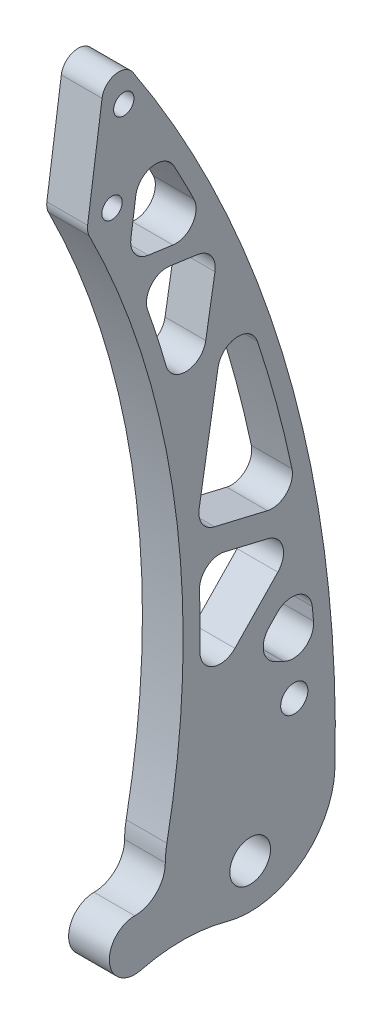
SolidWorks part; units mm, degrees
material "6061-T6 (SS)"
ref_plane "Front Plane" through (0, 0, 0) normal (0, 0, 1) x (1, 0, 0)
ref_plane "Top Plane" through (0, 0, 0) normal (0, 1, 0) x (1, 0, 0)
ref_plane "Right Plane" through (0, 0, 0) normal (1, 0, 0) x (0, 0, -1)
sketch "Sketch1" plane through (0, 0, 0) normal (1, 0, 0) x (0, 0, -1)
  line L0 (0, 0) -> (0, 200) construction
  line L1 (0, 0) -> (-44.9902, 194.874) construction
  line L2 (-41.8588, 217.155) -> (-48.1216, 172.593)
  circle A0 centre (0, -12) radius 6
  circle A1 centre (0, 0) radius 25
  arc A2 (24.9928, -0.6007) -> (-41.8588, 217.155) centre (-334.9033, 8.0499) ccw
  arc A3 (-24.539, 4.7789) -> (-48.1216, 172.593) centre (-279.7445, 54.4794) ccw
  dimension "D2" = 12
  dimension "D3" = 50
  dimension "D5" = 360
  dimension "D6" = 260
  dimension "D1" = 200
  dimension "D4" = 13
  dimension "D7" = 45
  dimension "D8" = 8
  dimension "D9" = 12
extrude "Boss-Extrude1" add sketch "Sketch1" along normal blind 12
sketch "Sketch3" plane through (12, 0, 0) normal (1, 0, 0) x (0, 0, -1)
  line L0 (-30.6472, 246.6326) -> (-44.1841, 150.313) construction
  line L1 (-41.8588, 217.155) -> (-48.1216, 172.593) construction
  circle A0 centre (-40.7145, 175) radius 3
  circle A1 centre (-37.2352, 199.7567) radius 3
  dimension "D2" = 6
  dimension "D1" = 25
  dimension "D3" = 7
  dimension "D4" = 175
extrude "Cut-Extrude2" cut sketch "Sketch3" against normal through all
sketch "Sketch4" plane through (12, 0, 0) normal (1, 0, 0) x (0, 0, -1)
  line L0 (-31.2609, 191.9692) -> (-35.9768, 158.4135)
  line L1 (-41.8588, 217.155) -> (-48.1216, 172.593) construction
  line L2 (-35.9768, 158.4135) -> (-11.7498, 155.0086)
  line L3 (-33.7602, 153.0529) -> (-9.3543, 149.6228)
  line L4 (-9.3543, 149.6228) -> (-18.1663, 96.9275)
  line L5 (-5.7303, 140.9792) -> (-15.9585, 79.8154)
  line L6 (-15.9585, 79.8154) -> (14.1619, 72.6915)
  line L7 (15.4681, 65.1894) -> (-15.3566, 72.4799)
  line L8 (15.4681, 65.1894) -> (-15.6193, 32.9646)
  line L10 (-2, 37) -> (16.7796, 56.4667)
  arc A2 (-19.6312, 3.8231) -> (-43.6673, 174.8644) centre (-279.7445, 54.4794) ccw
  arc A3 (-15.6193, 32.9646) -> (-35.9768, 158.4135) centre (-279.7445, 54.4794) ccw
  arc A4 (-15.6193, 32.9646) -> (19.7211, 24.3772) centre (-2, 12) cw
  arc A5 (19.9942, -0.4806) -> (-45.9289, 214.2508) centre (-334.9033, 8.0499) ccw
  arc A6 (19.7211, 24.3772) -> (-31.2609, 191.9692) centre (-334.9033, 8.0499) ccw
  dimension "D3" = 25
  dimension "D4" = 12
  dimension "D5" = 2
  dimension "D6" = 14
  dimension "D7" = 5
  dimension "D8" = 5
  dimension "D9" = 7
  dimension "D10" = 7
  dimension "D1" = 5
  dimension "D2" = 5
extrude "Cut-Extrude3" cut sketch "Sketch4" against normal through all contours L2 A6 L0 | A3 L4 L3 | L6 A6 L5 | A3 L8 L7 | A4 A6 L10
fillet "Fillet1" radius 6 15 edges at (6, 191.9692, 31.2609) (6, 155.0086, 11.7498) (6, 158.4135, 35.9768) (6, 153.0529, 33.7602) (6, 149.6228, 9.3543) (6, 96.9275, 18.1663) (6, 140.9792, 5.7303) (6, 72.6915, -14.1619) (6, 79.8154, 15.9585) (6, 72.4799, 15.3566) (6, 65.1894, -15.4681) (6, 32.9646, 15.6193) (6, 56.4667, -16.7796) (6, 37, 2) (6, 24.3772, -19.7211)
sketch "Sketch2" plane through (12, 0, 0) normal (1, 0, 0) x (0, 0, -1)
  line L0 (0, -12) -> (0, 208) construction
  circle A0 centre (13, 23) radius 4
  dimension "D3" = 8
  dimension "D2" = 35
  dimension "D1" = 220
  dimension "D4" = 13
extrude "Cut-Extrude1" cut sketch "Sketch2" against normal through all
sketch "Sketch5" plane through (12, 0, 0) normal (1, 0, 0) x (0, 0, -1)
  circle A0 centre (-34, -16.5) radius 7.5
  arc A2 (-34, -9) -> (-25, 0) centre (-34, 0) ccw
  arc A3 (-24.539, 4.7789) -> (24.9928, -0.6007) centre (0, 0) ccw construction
  arc A4 (-32.1775, -23.7752) -> (-6.6759, -24.0922) centre (-20.0276, -72.2765) cw
  dimension "D1" = 15
  dimension "D2" = 50
  dimension "D4" = 9
  dimension "D3" = 34
  dimension "D5" = 16.5
extrude "Boss-Extrude2" add sketch "Sketch5" against normal up to surface (12 mm away)
fillet "Fillet2" radius 5 2 edges at (6, 172.593, 48.1216) (6, 217.155, 41.8588)
